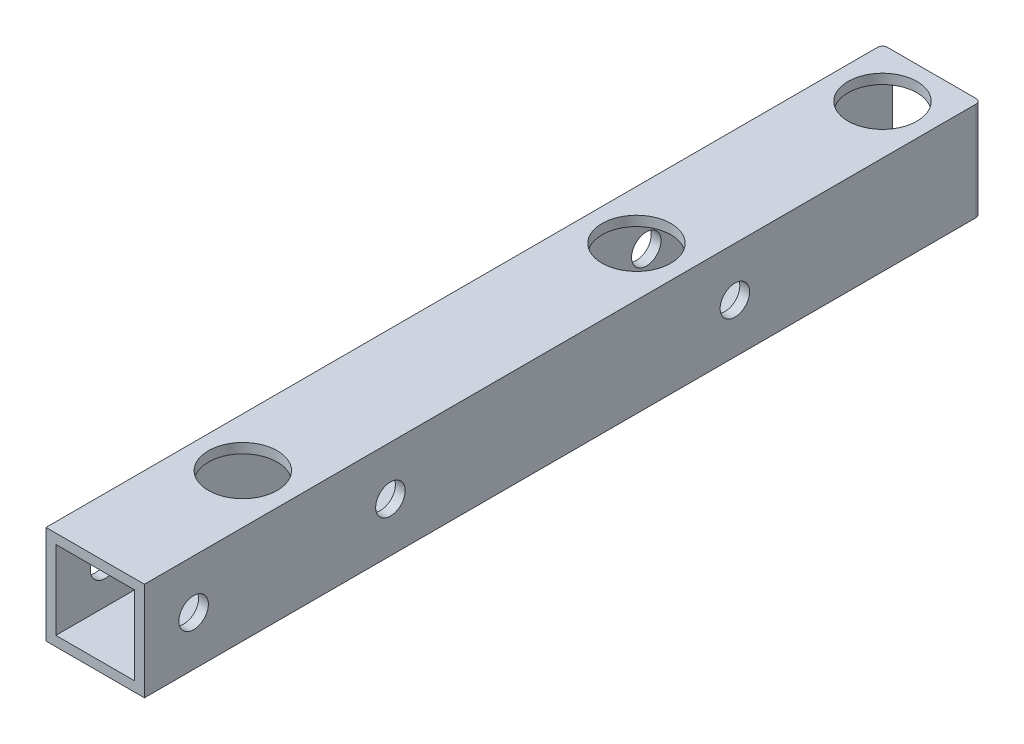
SolidWorks part; units mm, degrees
material "6063-O"
ref_plane "前视基准面" through (0, 0, 0) normal (0, 0, 1) x (1, 0, 0)
ref_plane "上视基准面" through (0, 0, 0) normal (0, 1, 0) x (1, 0, 0)
ref_plane "右视基准面" through (0, 0, 0) normal (1, 0, 0) x (0, 0, -1)
other "Configuration Table"
sketch "草图1" plane through (0, 0, 0) normal (0, 0, 1) x (1, 0, 0)
  line L1 (-5, 5) -> (5, 5)
  line L2 (-5, 5) -> (-5, -5)
  line L3 (-5, -5) -> (5, -5)
  line L4 (5, 5) -> (5, -5)
  line L5 (-5, 5) -> (5, -5) construction
  line L6 (-5, -5) -> (5, 5) construction
  point P4 (0, 0)
  dimension "D1" = 10
  dimension "D2" = 10
extrude "拉伸-薄壁1" add sketch "草图1" along normal blind 85 thin
sketch "草图2" plane through (0, 5, 0) normal (0, 1, 0) x (1, 0, 0)
  line L0 (0, -85) -> (0, 0) construction
  line L1 (5, -85) -> (-5, -85) construction
  line L2 (5, 0) -> (-5, 0) construction
  circle A1 centre (0, -70) radius 1.5
  circle A4 centre (0, -5) radius 1.5
  circle A5 centre (0, -30) radius 1.5
  dimension "D1" = 3
  dimension "D7" = 25
  dimension "D2" = 40
  dimension "D3" = 15
extrude "切除-拉伸1" cut sketch "草图2" against normal through all
sketch "草图3" plane through (-5, 0, 0) normal (-1, 0, 0) x (0, 0, 1)
  line L0 (85, -5) -> (75, 5) construction
  line L1 (85, 5) -> (0, 5) construction
  line L2 (75, 5) -> (85, 5) construction
  line L3 (85, 5) -> (85, -5) construction
  line L4 (0, 0) -> (85, 0) construction
  line L5 (0, 5) -> (0, -5) construction
  circle A0 centre (25, 0) radius 1.5
  circle A1 centre (60, 0) radius 1.5
  circle A2 centre (80, 0) radius 1.5
  dimension "D2" = 3
  dimension "D4" = 35
  dimension "D5" = 20
  dimension "D3" = 5
  dimension "D1" = 45
extrude "切除-拉伸2" cut sketch "草图3" against normal blind 10
sketch "草图4" plane through (0, 5, 0) normal (0, 1, 0) x (1, 0, 0)
  circle A0 centre (0, -5) radius 3.5
  circle A1 centre (0, -30) radius 3.5
  circle A2 centre (0, -70) radius 3.5
  dimension "D1" = 7
extrude "切除-拉伸3" cut sketch "草图4" against normal blind 5
fillet "圆角1" radius 0.5 2 edges at (-5, 0, 0) (5, 0, 0)
